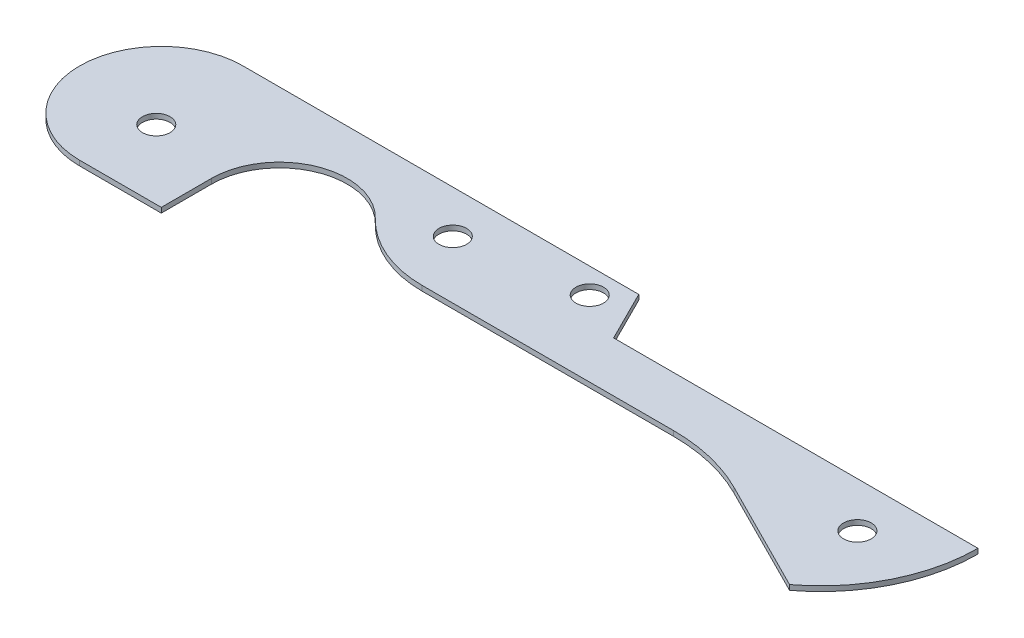
SolidWorks part; units mm, degrees
material "Stainless Steel (ferritic)"
ref_plane "Front Plane" through (0, 0, 0) normal (0, 0, 1) x (1, 0, 0)
ref_plane "Top Plane" through (0, 0, 0) normal (0, 1, 0) x (1, 0, 0)
ref_plane "Right Plane" through (0, 0, 0) normal (1, 0, 0) x (0, 0, -1)
sketch "Sketch1" plane through (0, 0, 0) normal (0, 1, 0) x (1, 0, 0)
  line L0 (0, 8.255) -> (40.005, 8.255)
  line L1 (40.005, 8.255) -> (42.545, 3.175)
  line L2 (42.545, 3.175) -> (79.375, 3.175)
  line L3 (73.025, -9.525) -> (61.6844, -3.8082)
  line L4 (53.6721, -1.905) -> (28.2721, -1.905)
  line L5 (8.255, -3.175) -> (8.255, -8.255)
  line L6 (0, -8.255) -> (8.255, -8.255)
  line L7 (79.375, 3.175) -> (79.375, -17.4302) construction
  arc A0 (0, 8.255) -> (0, -8.255) centre (0, 0) ccw
  arc A2 (61.6844, -3.8082) -> (53.6721, -1.905) centre (53.6809, -19.685) ccw
  arc A3 (28.2721, -1.905) -> (20.0476, 1.5875) centre (28.2721, 9.525) cw
  arc A4 (20.0476, 1.5875) -> (8.255, -3.175) centre (15.113, -3.175) ccw
  arc A5 (79.375, 3.175) -> (73.025, -9.525) centre (63.5, 3.175) cw
  point P20 (-8.255, 0)
  dimension "D1" = 16.51
  dimension "D10" = 17.78
  dimension "D12" = 11.43
  dimension "D14" = 6.35
  dimension "D2" = 48.26
  dimension "D3" = 87.63
  dimension "D4" = 36.83
  dimension "D5" = 10.16
  dimension "D6" = 5.08
  dimension "D7" = 12.7
  dimension "D8" = 4.572
  dimension "D9" = 12.7
  dimension "D11" = 5.08
  dimension "D13" = 25.4
extrude "Boss-Extrude1" add sketch "Sketch1" along normal blind 0.508
sketch "Sketch2" plane through (0, 0.508, 0) normal (0, 1, 0) x (1, 0, 0)
  line L0 (0, -8.255) -> (8.255, -8.255) construction
  line L3 (79.375, 3.175) -> (42.545, 3.175) construction
  line L4 (40.005, 8.255) -> (0, 8.255) construction
  circle A0 centre (0.762, -1.27) radius 1.397
  circle A1 centre (25.527, 3.937) radius 1.397
  circle A2 centre (37.592, 5.715) radius 1.397
  circle A3 centre (71.755, -1.397) radius 1.397
  arc A4 (0, 8.255) -> (0, -8.255) centre (0, 0) ccw construction
  dimension "D1" = 2.794
  dimension "D3" = 7.62
  dimension "D4" = 2.413
  dimension "D5" = 2.54
  dimension "D7" = 4.318
  dimension "D8" = 7.62
  dimension "D2" = 5.588
  dimension "D6" = 14.478
  dimension "D9" = 4.572
extrude "Cut-Extrude1" cut sketch "Sketch2" against normal through all
